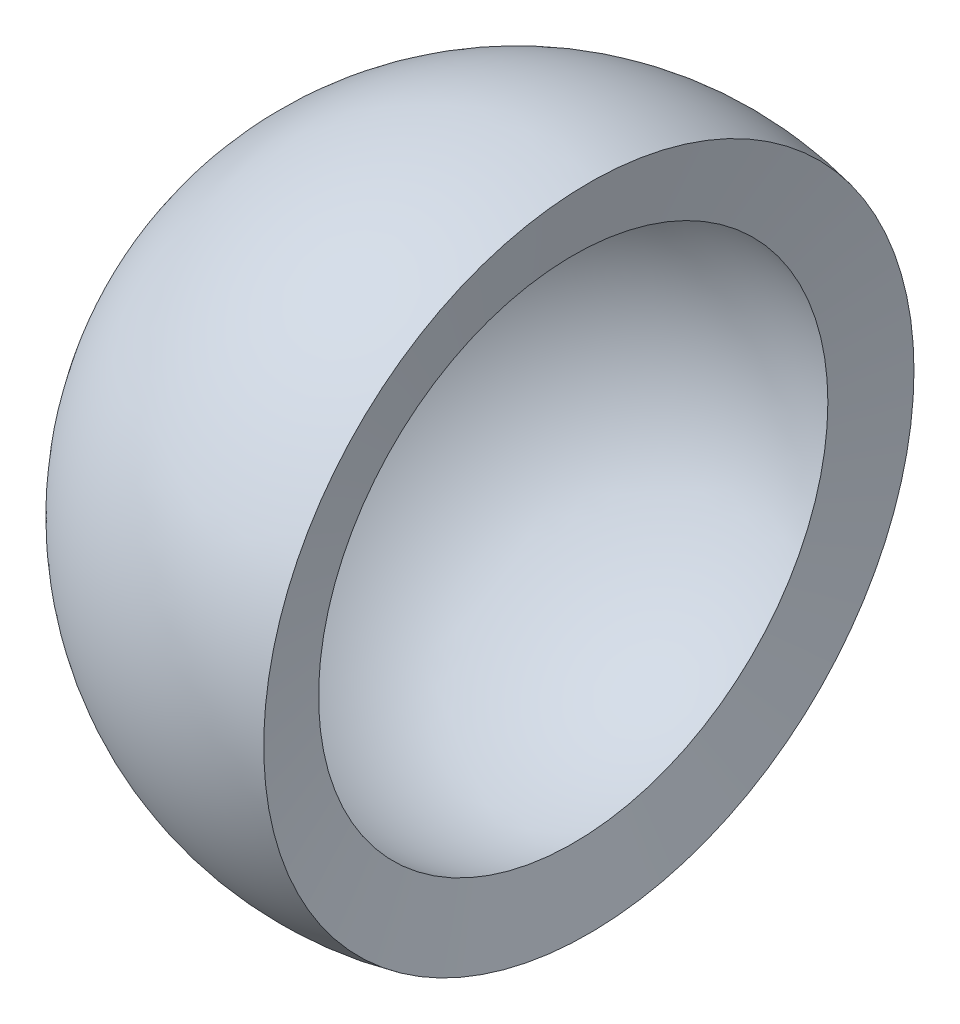
SolidWorks part; units mm, degrees
ref_plane "Alzado" through (0, 0, 0) normal (0, 0, 1) x (1, 0, 0)
ref_plane "Planta" through (0, 0, 0) normal (0, 1, 0) x (1, 0, 0)
ref_plane "Vista lateral" through (0, 0, 0) normal (1, 0, 0) x (0, 0, -1)
sketch "Croquis1" plane through (0, 0, 0) normal (0, 1, 0) x (1, 0, 0)
  line L0 (-19, 0) -> (-24.2598, 0)
  line L1 (4.1116, 18.5498) -> (5.2499, 23.6849)
  arc A0 (4.1116, 18.5498) -> (-19, 0) centre (0, 0) ccw
  arc A1 (5.2499, 23.6849) -> (-24.2598, 0) centre (0, 0) ccw
revolve "Revolución1" add sketch "Croquis1" angle 360 about L0
